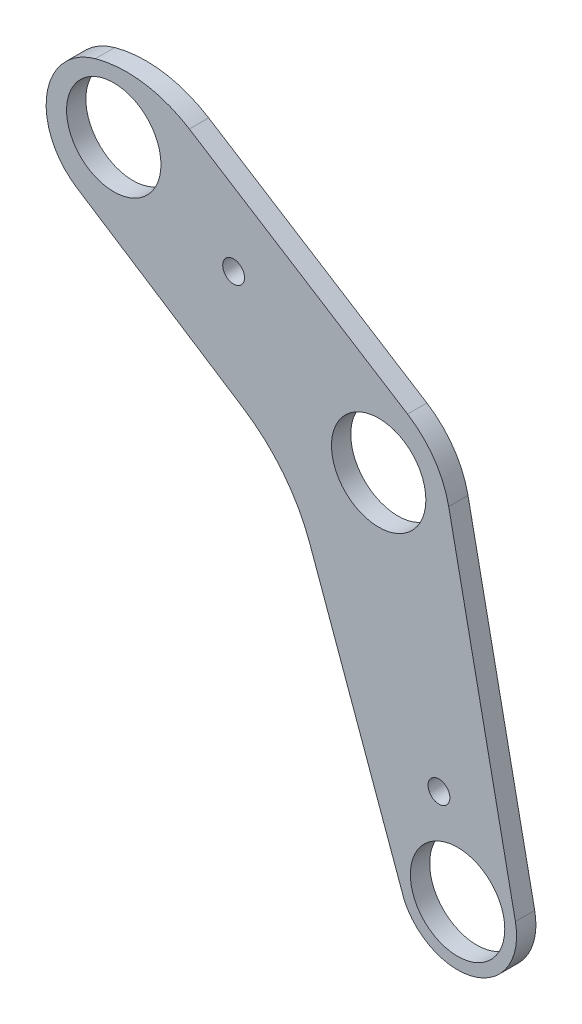
SolidWorks part; units mm, degrees
ref_plane "Front Plane" through (0, 0, 0) normal (0, 0, 1) x (1, 0, 0)
ref_plane "Top Plane" through (0, 0, 0) normal (0, 1, 0) x (1, 0, 0)
ref_plane "Right Plane" through (0, 0, 0) normal (1, 0, 0) x (0, 0, -1)
ref_plane "Plane1" through (0, 0, 0) normal (0, 0, -1) x (-1, 0, 0)
sketch "Sketch1" plane through (0, 0, 0) normal (0, 0, -1) x (-1, 0, 0)
  line L3 (165.7851, 142.9468) -> (130.9909, 174.5742)
  line L4 (130.9909, 174.5742) -> (31.9811, 112.057)
  line L23 (77.485, 85.8604) -> (165.7851, 142.9468)
  line L25 (31.9811, 112.057) -> (9.4092, 1.7104)
  line L29 (77.485, 85.8604) -> (43.0106, -9.6413)
  circle A1 centre (130.9909, 146.5103) radius 14.2875
  arc A4 (9.4092, 1.7104) -> (43.0106, -9.6413) centre (26.9175, -1.871) ccw
  circle A5 centre (32.554, 24.2134) radius 3.302
  circle A6 centre (94.7071, 129.4769) radius 3.302
  circle A10 centre (50.8, 98.679) radius 14.2875
  circle A11 centre (26.9175, -1.871) radius 14.2875
  point P11 (91.7114, 121.924)
  point P12 (87.2483, 127.6327)
  point P13 (94.7071, 129.4769)
  dimension "D1" = 28.575
  dimension "D2" = 28.575
  dimension "D3" = 6.604
  dimension "D4" = 6.604
extrude "Boss-Extrude1" add sketch "Sketch1" against normal blind 5.842
fillet "Fillet6" radius 35.56 1 edges at (-130.9909, 174.5742, 2.921)
fillet "Fillet10" radius 27.94 1 edges at (-31.9811, 112.057, 2.921)
fillet "Fillet13" radius 50.8 1 edges at (-77.485, 85.8604, 2.921)
fillet "Fillet16" radius 20.32 1 edges at (-165.7851, 142.9468, 2.921)
